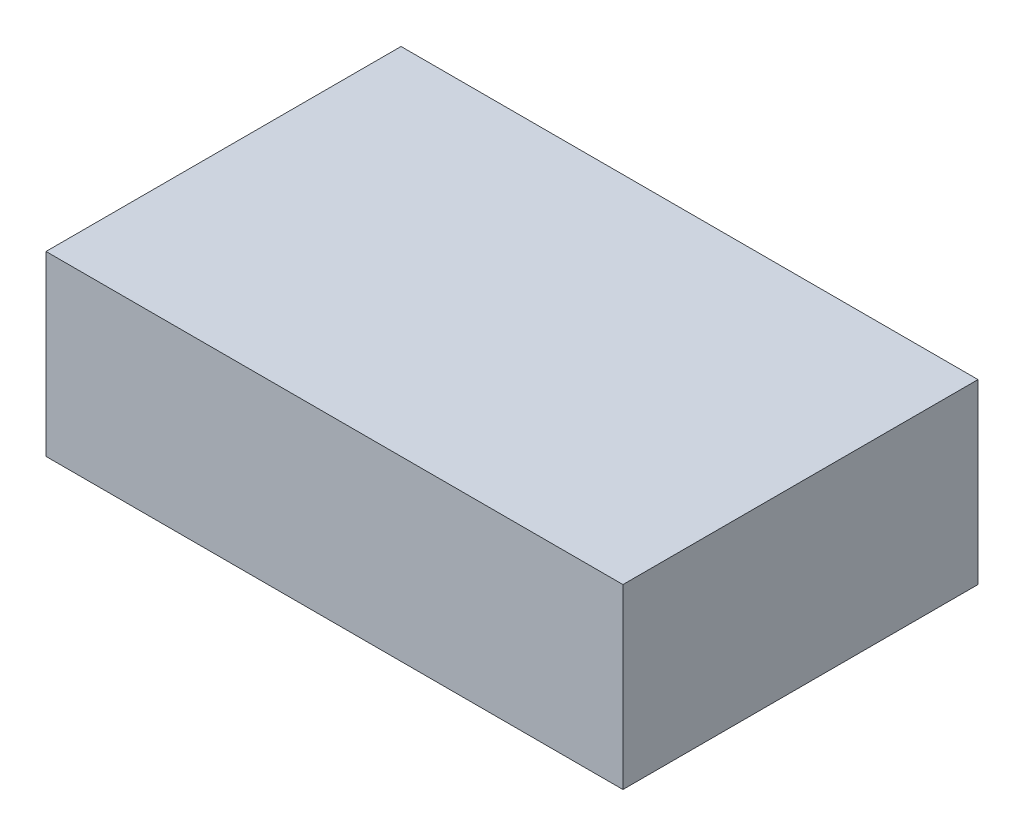
SolidWorks part; units mm, degrees
ref_plane "Front" through (0, 0, 0) normal (0, 0, 1) x (1, 0, 0)
ref_plane "Top" through (0, 0, 0) normal (0, 1, 0) x (1, 0, 0)
ref_plane "Right" through (0, 0, 0) normal (1, 0, 0) x (0, 0, -1)
sketch "Sketch1" plane through (0, 0, 0) normal (0, 1, 0) x (1, 0, 0)
  line L1 (0, 0) -> (1.3, 0)
  line L2 (0, 0) -> (0, 0.8)
  line L3 (0, 0.8) -> (1.3, 0.8)
  line L4 (1.3, 0) -> (1.3, 0.8)
  line L5 (0, 0) -> (1.3, 0.8) construction
  line L6 (0, 0.8) -> (1.3, 0) construction
  point P4 (0.65, 0.4)
  dimension "D1" = 1.3
  dimension "D2" = 0.8
extrude "Boss-Extrude1" add sketch "Sketch1" along normal blind 0.4 contours L3 L4 L1 L2
